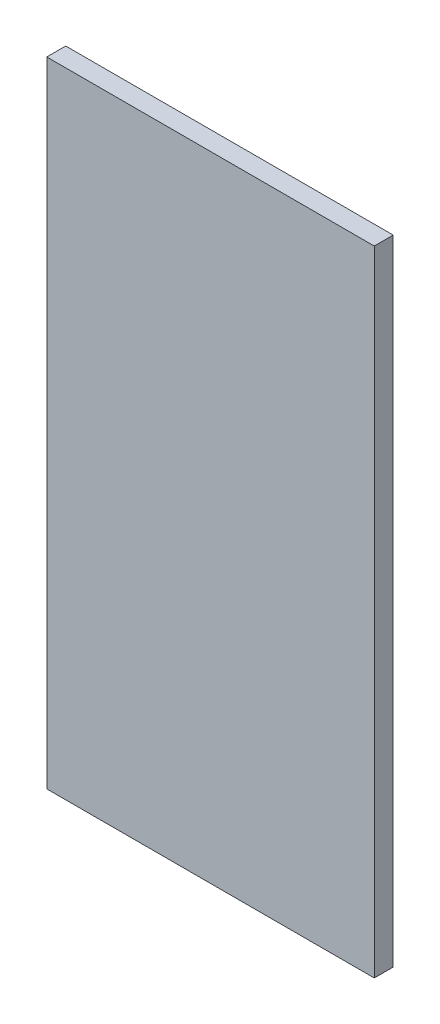
SolidWorks part; units mm, degrees
ref_plane "Front Plane" through (0, 0, 0) normal (0, 0, 1) x (1, 0, 0)
ref_plane "Top Plane" through (0, 0, 0) normal (0, 1, 0) x (1, 0, 0)
ref_plane "Right Plane" through (0, 0, 0) normal (1, 0, 0) x (0, 0, -1)
sketch "Sketch1" plane through (0, 0, 0) normal (0, 0, 1) x (1, 0, 0)
  line L1 (155.5, -301) -> (-155.5, -301)
  line L2 (155.5, -301) -> (155.5, 301)
  line L3 (155.5, 301) -> (-155.5, 301)
  line L4 (-155.5, -301) -> (-155.5, 301)
  line L5 (155.5, -301) -> (-155.5, 301) construction
  line L6 (155.5, 301) -> (-155.5, -301) construction
  point P0 (0, 0)
  dimension "D1" = 602
  dimension "D2" = 311
extrude "Boss-Extrude1" add sketch "Sketch1" along normal blind 18
equation "\"H_DSP\"=18"
equation "\"D1@Boss-Extrude1\"=\"H_DSP\""
